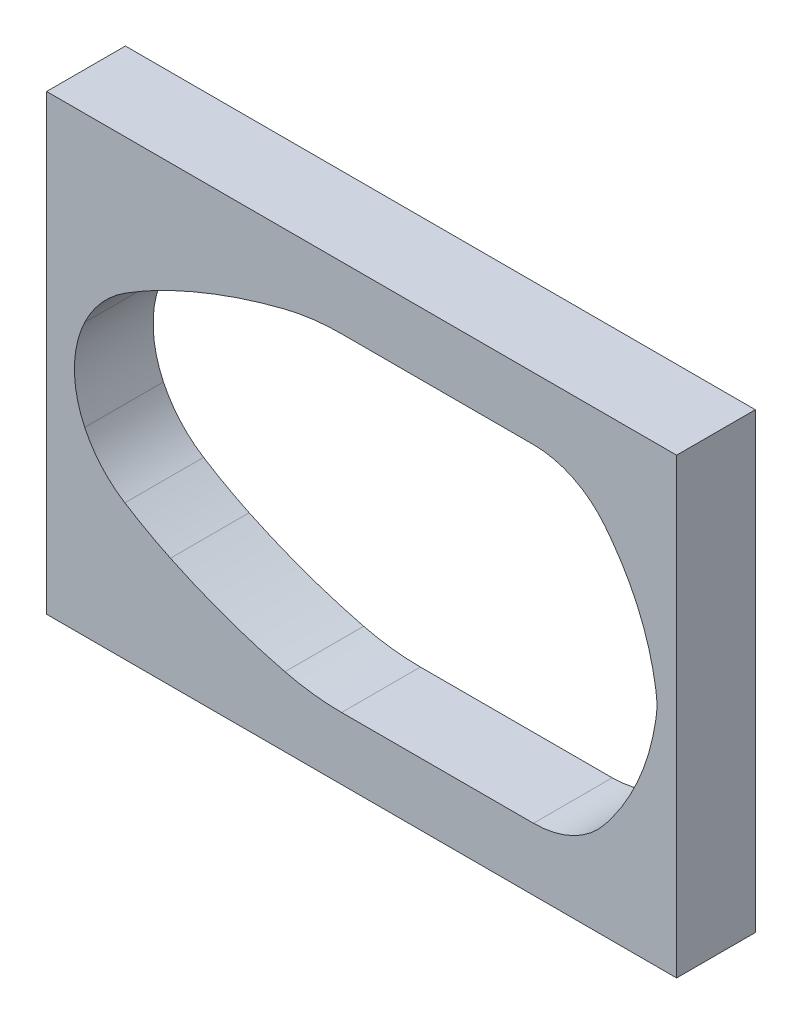
SolidWorks part; units mm, degrees
ref_plane "前基準面" through (0, 0, 0) normal (0, 0, 1) x (1, 0, 0)
ref_plane "上基準面" through (0, 0, 0) normal (0, 1, 0) x (1, 0, 0)
ref_plane "右基準面" through (0, 0, 0) normal (1, 0, 0) x (0, 0, -1)
sketch "草圖2" plane through (0, 0, 0) normal (0, 0, 1) x (1, 0, 0)
  line L0 (-46.4388, 70.8926) -> (220.2278, 70.8926) construction
  line L1 (-105.3201, 72.5991) -> (290.3658, 72.5991) construction
  line L3 (9.5822, 114.2394) -> (32.6396, 114.2394)
  line L4 (32.6396, 114.2394) -> (35.912, 114.2394)
  line L16 (89.3434, 76.1268) -> (89.4509, 75.4079)
  line L17 (89.3434, 69.0713) -> (89.4509, 69.7903)
  line L29 (32.6396, 30.9588) -> (35.912, 30.9588)
  line L30 (9.5822, 30.9588) -> (32.6396, 30.9588)
  line L31 (58.3023, 114.2394) -> (35.912, 114.2394)
  line L32 (58.3023, 30.9588) -> (35.912, 30.9588)
  arc A1 (-45.4817, 95.653) -> (-33.9004, 102.0463) centre (13.2691, 2.9136) cw
  arc A2 (-33.9004, 102.0463) -> (-4.818, 112.4717) centre (32.6396, -37.7959) cw
  arc A3 (-4.818, 112.4717) -> (9.5822, 114.2394) centre (9.5822, 54.703) cw
  arc A4 (58.3023, 114.2394) -> (76.3982, 105.4778) centre (58.3023, 91.1712) cw
  arc A5 (76.3982, 105.4778) -> (78.3509, 102.9079) centre (10.4589, 53.3467) cw
  arc A6 (78.3509, 102.9079) -> (89.3434, 76.1268) centre (29.3855, 67.1631) cw
  arc A7 (89.4509, 75.4079) -> (89.4509, 69.7903) centre (70.6632, 72.5991) cw
  arc A8 (78.3509, 42.2903) -> (89.3434, 69.0713) centre (29.3855, 78.0351) ccw
  arc A9 (76.3982, 39.7204) -> (78.3509, 42.2903) centre (10.4589, 91.8515) ccw
  arc A10 (58.3023, 30.9588) -> (76.3982, 39.7204) centre (58.3023, 54.0269) ccw
  arc A11 (-4.818, 32.7265) -> (9.5822, 30.9588) centre (9.5822, 90.4952) ccw
  arc A12 (-33.9004, 43.1519) -> (-4.818, 32.7265) centre (32.6396, 182.9941) ccw
  arc A13 (-45.4817, 49.5452) -> (-33.9004, 43.1519) centre (13.2691, 142.2846) ccw
  arc A15 (-45.4817, 95.653) -> (-55.6776, 84.157) centre (-30.6332, 72.2143) ccw
  arc A16 (-55.6776, 84.157) -> (-55.6776, 61.0412) centre (-31.4402, 72.5991) ccw
  arc A17 (-45.4817, 49.5452) -> (-55.6776, 61.0412) centre (-30.6332, 72.9839) cw
  point P62 (-51.3914, 90.6249)
  point P64 (-53.497, 72.5991)
  point P65 (-51.3914, 54.5733)
  dimension "D1" = 83.2806
sketch "草圖4" plane through (0, 0, 0) normal (0, 0, 1) x (1, 0, 0)
  line L0 (-105.3201, 72.5991) -> (290.3658, 72.5991) construction
  line L1 (-65.3403, 130.0991) -> (94.6597, 130.0991)
  line L2 (-65.3403, 130.0991) -> (-65.3403, 15.0991)
  line L3 (-65.3403, 15.0991) -> (94.6597, 15.0991)
  line L4 (94.6597, 130.0991) -> (94.6597, 15.0991)
  arc A0 (89.4509, 69.7903) -> (89.4509, 75.4079) centre (70.6632, 72.5991) ccw construction
  point P9 (89.6597, 72.5991)
  dimension "D1" = 160
  dimension "D2" = 115
  dimension "D3" = 57.5
  dimension "D4" = 5
extrude "填料-伸長1" add sketch "草圖4" along normal blind 20 contours L4 L3 L2 L1
extrude "除料-伸長1" cut sketch "草圖2" along normal blind 20
ref_plane "平面1" through (-66.2, 0, 0) normal (1, 0, 0) x (0, 0, -1)
sketch "草圖6" plane through (-66.2, 0, 0) normal (1, 0, 0) x (0, 0, -1)
  line L0 (-10, 130.0991) -> (-10, 15.0991) construction
  line L1 (-20, 130.0991) -> (0, 130.0991) construction
  line L2 (-20, 15.0991) -> (0, 15.0991) construction
  line L3 (-20, 72.5991) -> (0, 72.5991) construction
  line L4 (-20, 130.0991) -> (-20, 15.0991) construction
  line L5 (0, 130.0991) -> (0, 15.0991) construction
  circle A0 centre (-10, 120.0991) radius 5
  circle A1 centre (-10, 105.0991) radius 5
  circle A2 centre (-10, 40.0991) radius 5
  circle A3 centre (-10, 25.0991) radius 5
  dimension "D1" = 10
  dimension "D2" = 5
  dimension "D5" = 5
sketch "草圖16" plane through (-66.2, 0, 0) normal (1, 0, 0) x (0, 0, -1)
  line L0 (-20, 72.5991) -> (0, 72.5991) construction
  line L1 (-10, 130.0991) -> (-10, 15.0991) construction
  circle A0 centre (-10, 120.0991) radius 5.5
  circle A1 centre (-10, 105.0991) radius 5.5
  circle A2 centre (-10, 40.0991) radius 5.5
  circle A3 centre (-10, 25.0991) radius 5.5
  dimension "D1" = 11
  dimension "D2" = 11
extrude "除料-伸長2" cut sketch "草圖16" along normal blind 15 contours A2 | A1 | A0 | A3
